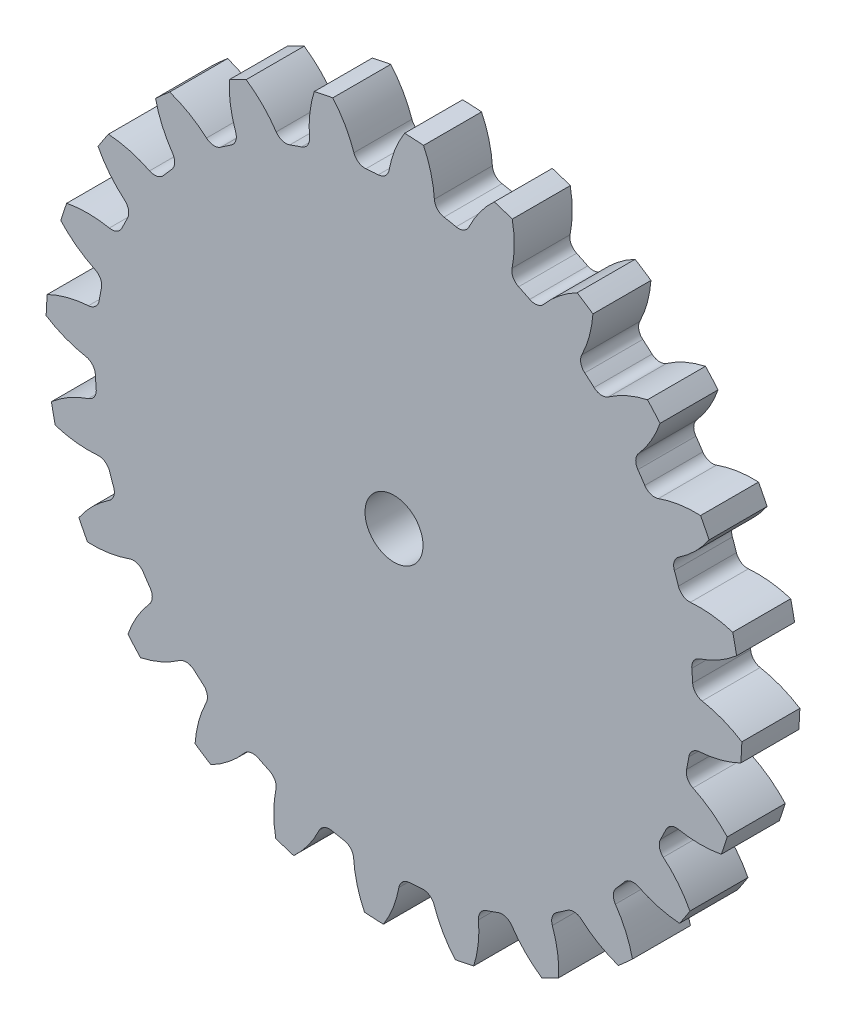
SolidWorks part; units mm, degrees
ref_plane "Alzado" through (0, 0, 0) normal (0, 0, 1) x (1, 0, 0)
ref_plane "Planta" through (0, 0, 0) normal (0, 1, 0) x (1, 0, 0)
ref_plane "Vista lateral" through (0, 0, 0) normal (1, 0, 0) x (0, 0, -1)
sketch "Croquis1" plane through (0, 0, 0) normal (0, 0, 1) x (1, 0, 0)
  circle A0 centre (0, 0) radius 30
  dimension "D1" = 60
extrude "Saliente-Extruir1" add sketch "Croquis1" along normal mid plane 5
sketch "Croquis2" plane through (0, 0, 2.5) normal (0, 0, 1) x (1, 0, 0)
  arc A0 (0.9153, 29.986) -> (-5.278, 29.5321) centre (0, 0) ccw
  arc A2 (-1.3543, 25.7472) -> (-2.4146, 25.6694) centre (0, 0) ccw
  arc A3 (0.9153, 29.986) -> (-0.4231, 26.5658) centre (9.0392, 24.835) ccw
  arc A4 (-5.278, 29.5321) -> (-3.4552, 26.3436) centre (-12.564, 23.2515) cw
  arc A5 (-0.4231, 26.5658) -> (-1.3543, 25.7472) centre (-1.4068, 26.7458) cw
  arc A6 (-3.4552, 26.3436) -> (-2.4146, 25.6694) centre (-2.5083, 26.665) ccw
  dimension "D1" = 51.5655
  dimension "D2" = 1
  dimension "D3" = 60
extrude "Cortar-Extruir1" cut sketch "Croquis2" against normal through all
pattern_circular "MatrizC1" count 24 every 15 about axis through (0, 0, 0) along (0, 0, 1) of "Cortar-Extruir1"
sketch "Croquis3" plane through (0, 0, 2.5) normal (0, 0, 1) x (1, 0, 0)
  circle A0 centre (0, 0) radius 2.5
  dimension "D1" = 5
extrude "Cortar-Extruir2" cut sketch "Croquis3" against normal through all
